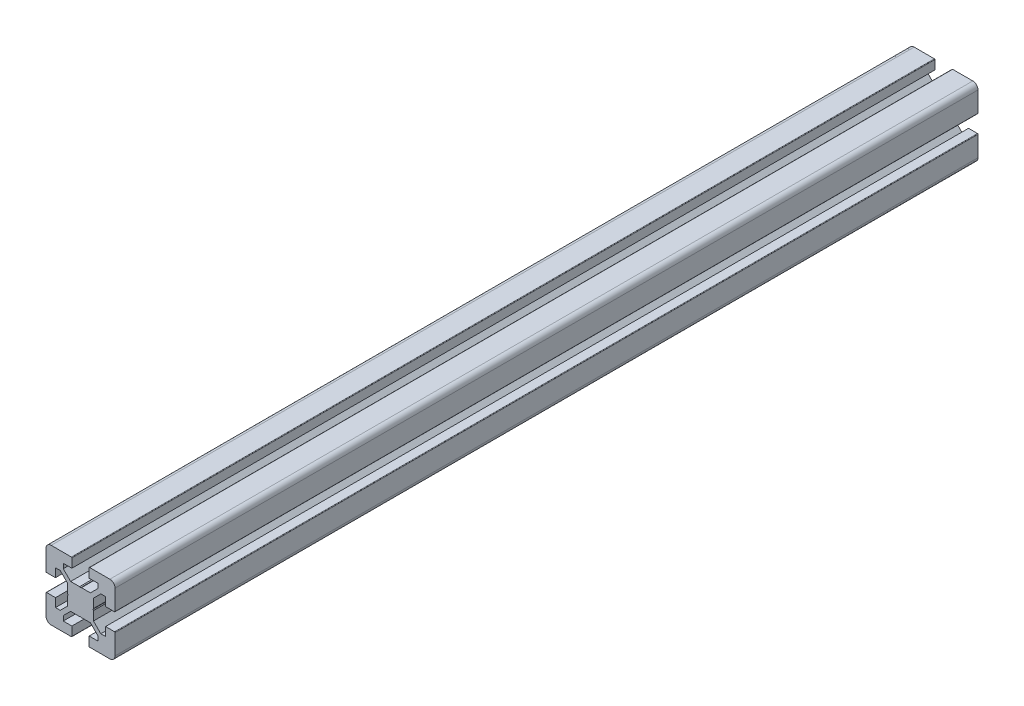
SolidWorks part; units mm, degrees
ref_plane "正面" through (0, 0, 0) normal (0, 0, 1) x (1, 0, 0)
ref_plane "平面" through (0, 0, 0) normal (0, 1, 0) x (1, 0, 0)
ref_plane "右側面" through (0, 0, 0) normal (1, 0, 0) x (0, 0, -1)
sketch "Model" plane through (0, 0, 0) normal (0, 0, 1) x (1, 0, 0)
  line L0 (160, 30) -> (160, 70)
  line L1 (110, 70) -> (110, 30)
  line L2 (160, 30) -> (110, 30)
  line L3 (110, 55) -> (160, 55)
  line L4 (110, 45) -> (160, 45)
  line L5 (160, 70) -> (110, 70)
  line L6 (105, 50) -> (165, 50) construction
  line L7 (110, 50.5196) -> (160, 50.5196)
  line L8 (110, 49.4804) -> (160, 49.4804)
  line L9 (110, 60) -> (160, 60) construction
  line L10 (110, 40) -> (160, 40) construction
  line L11 (37, 68) -> (33, 68)
  line L12 (69.7, 55) -> (64.5, 55)
  line L13 (64.5, 60) -> (64.5, 55)
  line L14 (70, 67) -> (70, 55.3)
  line L15 (68, 67) -> (68, 63)
  line L16 (64.5, 40) -> (64.5, 45)
  line L17 (69.7, 45) -> (64.5, 45)
  line L18 (70, 33) -> (70, 44.7)
  line L19 (68, 33) -> (68, 37)
  line L20 (33, 70) -> (44.7, 70)
  line L21 (60, 64.5) -> (60, 61.7678)
  line L22 (60, 64.5) -> (55, 64.5)
  line L23 (60, 61.7678) -> (55.7322, 57.5)
  line L24 (61.7678, 60) -> (57.5, 55.7322)
  line L25 (40, 64.5) -> (40, 61.7678)
  line L26 (40, 64.5) -> (45, 64.5)
  line L27 (40, 61.7678) -> (44.2678, 57.5)
  line L28 (35.5, 60) -> (38.2322, 60)
  line L29 (30.3, 55) -> (35.5, 55)
  line L30 (38.2322, 60) -> (42.5, 55.7322)
  line L31 (35.5, 55) -> (35.5, 60)
  line L32 (30, 67) -> (30, 55.3)
  line L33 (32, 67) -> (32, 63)
  line L34 (38, 67) -> (38, 63)
  line L35 (45, 69.7) -> (45, 64.5)
  line L36 (55, 69.7) -> (55, 64.5)
  line L37 (62, 67) -> (62, 63)
  line L38 (61.7678, 40) -> (57.5, 44.2678)
  line L39 (60, 35.5) -> (60, 38.2322)
  line L40 (60, 38.2322) -> (55.7322, 42.5)
  line L41 (55, 30.3) -> (55, 35.5)
  line L42 (62, 33) -> (62, 37)
  line L43 (38.2322, 40) -> (42.5, 44.2678)
  line L44 (40, 35.5) -> (40, 38.2322)
  line L45 (40, 35.5) -> (45, 35.5)
  line L46 (44.2678, 42.5) -> (49.4804, 42.5)
  line L47 (40, 38.2322) -> (44.2678, 42.5)
  line L48 (35.5, 45) -> (35.5, 40)
  line L49 (30.3, 45) -> (35.5, 45)
  line L50 (33, 38) -> (37, 38)
  line L51 (35.5, 40) -> (38.2322, 40)
  line L52 (33, 32) -> (37, 32)
  line L53 (33, 30) -> (44.7, 30)
  line L54 (30, 33) -> (30, 44.7)
  line L55 (32, 33) -> (32, 37)
  line L56 (38, 33) -> (38, 37)
  line L57 (45, 30.3) -> (45, 35.5)
  line L58 (50, 75) -> (50, 25) construction
  line L59 (57.5, 55.7322) -> (57.5, 50.5196)
  line L60 (67, 38) -> (63, 38)
  line L61 (25, 50) -> (75, 50) construction
  line L62 (64.5, 40) -> (61.7678, 40)
  line L63 (67, 62) -> (63, 62)
  line L64 (64.5, 60) -> (61.7678, 60)
  line L65 (42.5, 44.2678) -> (42.5, 49.4804)
  line L66 (37, 62) -> (33, 62)
  line L67 (44.2678, 57.5) -> (49.4804, 57.5)
  line L68 (57.5, 49.4804) -> (57.5, 44.2678)
  line L69 (42.5, 50.5196) -> (42.5, 55.7322)
  line L70 (50.5196, 57.5) -> (55.7322, 57.5)
  line L71 (55.3, 70) -> (67, 70)
  line L72 (63, 68) -> (67, 68)
  line L73 (55.3, 30) -> (67, 30)
  line L74 (63, 32) -> (67, 32)
  line L75 (55, 35.5) -> (60, 35.5)
  line L76 (50.5196, 42.5) -> (55.7322, 42.5)
  line L77 (57.2, 50) -> (57.5, 50.5196)
  line L78 (57.2, 50) -> (57.5, 49.4804)
  line L79 (42.8, 50) -> (42.5, 50.5196)
  line L80 (42.8, 50) -> (42.5, 49.4804)
  line L81 (50, 57.2) -> (49.4804, 57.5)
  line L82 (50, 57.2) -> (50.5196, 57.5)
  line L83 (50, 42.8) -> (49.4804, 42.5)
  line L84 (50, 42.8) -> (50.5196, 42.5)
  arc A0 (69.7, 55) -> (70, 55.3) centre (69.7, 55.3) ccw
  arc A1 (68, 67) -> (67, 68) centre (67, 67) ccw
  arc A2 (70, 44.7) -> (69.7, 45) centre (69.7, 44.7) ccw
  arc A3 (68, 37) -> (67, 38) centre (67, 37) ccw
  arc A4 (62, 63) -> (63, 62) centre (63, 63) ccw
  arc A5 (30, 55.3) -> (30.3, 55) centre (30.3, 55.3) ccw
  arc A6 (37, 62) -> (38, 63) centre (37, 63) ccw
  arc A7 (38, 67) -> (37, 68) centre (37, 67) ccw
  arc A8 (62, 33) -> (63, 32) centre (63, 33) ccw
  arc A9 (30.3, 45) -> (30, 44.7) centre (30.3, 44.7) ccw
  arc A10 (38, 37) -> (37, 38) centre (37, 37) ccw
  arc A11 (32, 33) -> (33, 32) centre (33, 33) ccw
  arc A12 (37, 32) -> (38, 33) centre (37, 33) ccw
  arc A13 (33, 38) -> (32, 37) centre (33, 37) ccw
  arc A14 (63, 38) -> (62, 37) centre (63, 37) ccw
  arc A15 (67, 62) -> (68, 63) centre (67, 63) ccw
  arc A16 (30, 33) -> (33, 30) centre (33, 33) ccw
  arc A17 (44.7, 30) -> (45, 30.3) centre (44.7, 30.3) ccw
  arc A18 (32, 63) -> (33, 62) centre (33, 63) ccw
  arc A19 (33, 68) -> (32, 67) centre (33, 67) ccw
  arc A20 (45, 69.7) -> (44.7, 70) centre (44.7, 69.7) ccw
  arc A21 (33, 70) -> (30, 67) centre (33, 67) ccw
  arc A22 (63, 68) -> (62, 67) centre (63, 67) ccw
  arc A23 (67, 32) -> (68, 33) centre (67, 33) ccw
  arc A24 (55, 30.3) -> (55.3, 30) centre (55.3, 30.3) ccw
  arc A25 (55.3, 70) -> (55, 69.7) centre (55.3, 69.7) ccw
  arc A26 (67, 30) -> (70, 33) centre (67, 33) ccw
  arc A27 (70, 67) -> (67, 70) centre (67, 67) ccw
  arc A28 (45.694, 53.0035) -> (45.694, 46.9966) centre (50, 50) ccw
  arc A29 (46.9981, 45.6929) -> (53.0039, 45.6943) centre (50, 50) ccw
  arc A30 (54.3061, 46.9967) -> (54.3061, 53.0034) centre (50, 50) ccw
  arc A31 (53.0033, 54.3061) -> (46.9968, 54.3062) centre (50, 50) ccw
  arc A32 (46.4038, 54.6058) -> (45.3944, 53.5962) centre (45.4038, 54.5962) ccw
  arc A33 (54.608, 53.5963) -> (53.5962, 54.6065) centre (54.5962, 54.5962) ccw
  arc A34 (53.5962, 45.3942) -> (54.6061, 46.4038) centre (54.5962, 45.4038) ccw
  arc A35 (45.3939, 46.4037) -> (46.4038, 45.3942) centre (45.4038, 45.4038) ccw
  arc A36 (45.694, 53.0035) -> (45.3944, 53.5962) centre (45.3778, 53.2158) ccw
  arc A37 (46.4038, 54.6058) -> (46.9968, 54.3062) centre (46.7842, 54.6222) ccw
  arc A38 (54.608, 53.5963) -> (54.3061, 53.0034) centre (54.6221, 53.2158) ccw
  arc A39 (53.0033, 54.3061) -> (53.5962, 54.6065) centre (53.2158, 54.6221) ccw
  arc A40 (45.3939, 46.4037) -> (45.694, 46.9966) centre (45.3778, 46.7842) ccw
  arc A41 (46.9981, 45.6929) -> (46.4038, 45.3942) centre (46.7842, 45.3779) ccw
  arc A42 (54.3061, 46.9967) -> (54.6061, 46.4038) centre (54.6222, 46.7842) ccw
  arc A43 (53.5962, 45.3942) -> (53.0039, 45.6943) centre (53.2158, 45.3778) ccw
  text T0 "HFS84040" font "SWTXT" height 4
  text T1 "HFS8-4040-50" font "SWTXT" height 4
extrude "ﾎﾞｽ - 押し出し1" add sketch "Model" against normal blind 500 contours L20 A20 L35 L26 L25 L27 L67 L81 L82 L70 L23 L21 L22 L36 A25 L71 A27 L14 A0 L12 L13 L64 L24 L59 L77 L78 L68 L38 L62 L16 L17 A2 L18 A26 L73 A24 L41 L75 L39 L40 L76 L84 L83 L46 L47 L44 L45 L57 A17 L53 A16 L54 A9 L49 L48 L51 L43 L65 L80 L79 L69 L30 L28 L31 L29 A5 L32 A21
